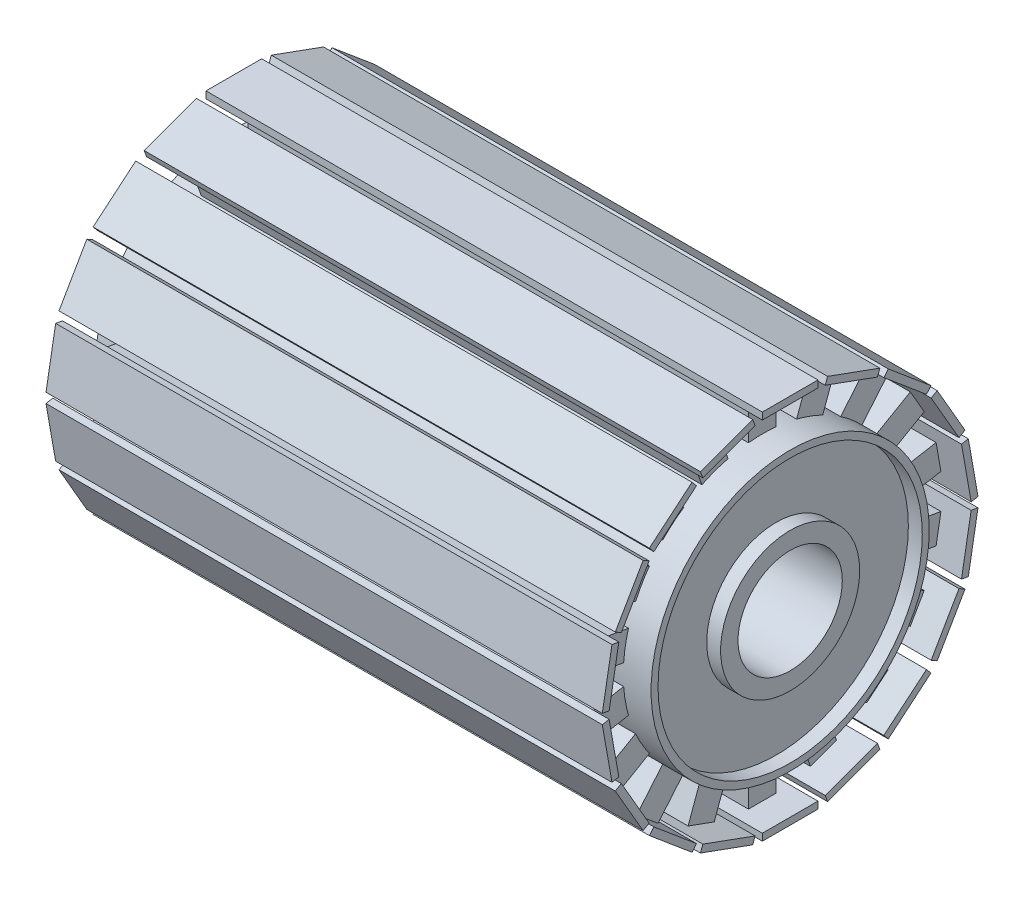
SolidWorks part; units mm, degrees
ref_plane "Front Plane" through (0, 0, 0) normal (0, 0, 1) x (1, 0, 0)
ref_plane "Top Plane" through (0, 0, 0) normal (0, 1, 0) x (1, 0, 0)
ref_plane "Right Plane" through (0, 0, 0) normal (1, 0, 0) x (0, 0, -1)
sketch "Sketch1" plane through (0, 0, 0) normal (1, 0, 0) x (0, 0, -1)
  circle A0 centre (0, 0) radius 25.4
  dimension "D1" = 50.8
extrude "Boss-Extrude1" add sketch "Sketch1" along normal mid plane 101.6
sketch "Sketch2" plane through (50.8, 0, 0) normal (1, 0, 0) x (0, 0, -1)
  circle A0 centre (0, 0) radius 24.13
  circle A1 centre (0, 0) radius 12.7
  dimension "D1" = 48.26
  dimension "D2" = 25.4
extrude "Cut-Extrude1" cut sketch "Sketch2" against normal blind 2.54
sketch "Sketch3" plane through (-50.8, 0, 0) normal (-1, 0, 0) x (0, 0, 1)
  circle A1 centre (0, 0) radius 24.13
  circle A2 centre (0, 0) radius 12.7
  dimension "D1" = 48.26
extrude "Cut-Extrude2" cut sketch "Sketch3" against normal blind 2.54
sketch "Sketch4" plane through (0, 0, 0) normal (1, 0, 0) x (0, 0, -1)
  line L1 (-2.54, 32.6711) -> (2.54, 32.6711)
  line L2 (-2.54, 32.6711) -> (-2.54, 25.0511)
  line L3 (-2.54, 25.0511) -> (2.54, 25.0511)
  line L4 (2.54, 32.6711) -> (2.54, 25.0511)
  line L5 (-2.54, 32.6711) -> (2.54, 25.0511) construction
  line L6 (-2.54, 25.0511) -> (2.54, 32.6711) construction
  point P0 (0, 28.8611)
  dimension "D1" = 5.08
  dimension "D2" = 7.62
extrude "Boss-Extrude2" add sketch "Sketch4" along normal mid plane 91.44
sketch "Sketch5" plane through (0, 32.6711, 0) normal (0, 1, 0) x (1, 0, 0)
  line L1 (-50.8, -5.08) -> (50.8, -5.08)
  line L2 (-50.8, -5.08) -> (-50.8, 5.08)
  line L3 (-50.8, 5.08) -> (50.8, 5.08)
  line L4 (50.8, -5.08) -> (50.8, 5.08)
  line L5 (-50.8, -5.08) -> (50.8, 5.08) construction
  line L6 (-50.8, 5.08) -> (50.8, -5.08) construction
  point P0 (0, 0)
  dimension "D1" = 101.6
  dimension "D2" = 10.16
extrude "Boss-Extrude3" add sketch "Sketch5" along normal blind 1.27
pattern_circular "CirPattern1" count 18 over 360 about axis through (0, 0, 0) along (1, 0, 0) of "Boss-Extrude3", "Boss-Extrude2"
sketch "Sketch6" plane through (50.8, 0, 0) normal (1, 0, 0) x (0, 0, -1)
  circle A0 centre (0, 0) radius 9.525
extrude "Cut-Extrude3" cut sketch "Sketch6" against normal through all both and the other way through all
